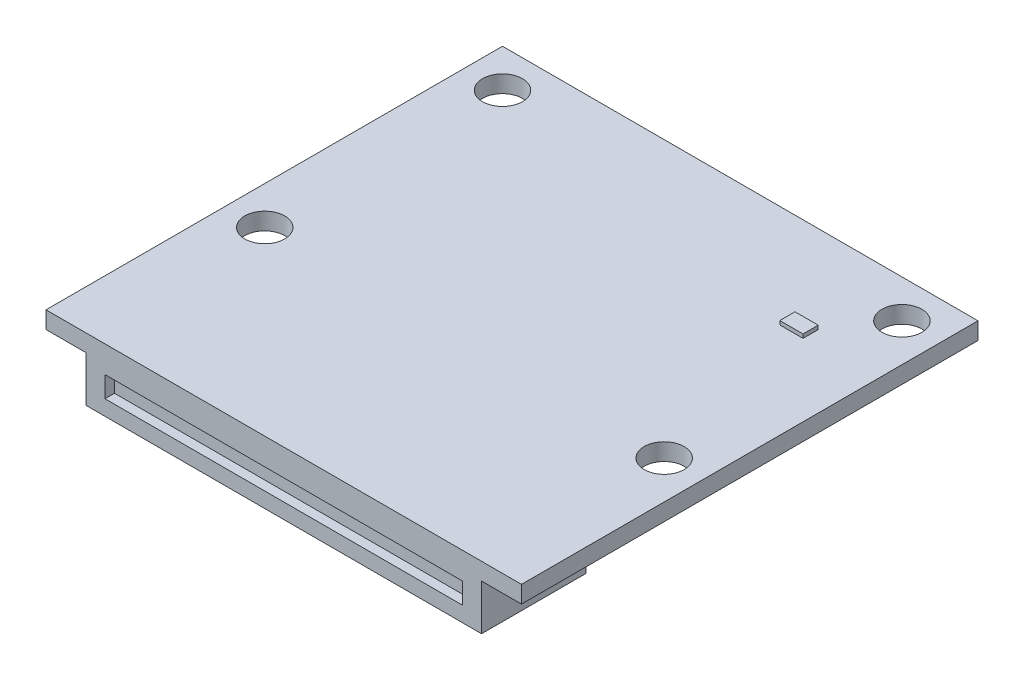
SolidWorks part; units mm, degrees
material "Epoxid, Ungefüllt"
ref_plane "Vorne" through (0, 0, 0) normal (0, 0, 1) x (1, 0, 0)
ref_plane "Oben" through (0, 0, 0) normal (0, 1, 0) x (1, 0, 0)
ref_plane "Rechts" through (0, 0, 0) normal (1, 0, 0) x (0, 0, -1)
sketch "Skizze1" plane through (0, 0, 0) normal (0, 1, 0) x (1, 0, 0)
  line L0 (0, 14.5) -> (0, -9.5) construction
  line L1 (-12.5, 14.5) -> (12.5, 14.5)
  line L2 (-12.5, 14.5) -> (-12.5, -9.5)
  line L3 (-12.5, -9.5) -> (12.5, -9.5)
  line L4 (12.5, 14.5) -> (12.5, -9.5)
extrude "PCB" add sketch "Skizze1" against normal blind 0.9
sketch "Skizze2" plane through (0, 0, 0) normal (0, 1, 0) x (1, 0, 0)
  line L0 (12.5, 14.5) -> (-12.5, 14.5) construction
  line L1 (12.5, -9.5) -> (12.5, 14.5) construction
  line L2 (0, 0) -> (0, 9.3158) construction
  circle A0 centre (10.5, 12.5) radius 1.05
  circle A1 centre (10.5, 0) radius 1.05
  circle A2 centre (-10.5, 0) radius 1.05
  circle A3 centre (-10.5, 12.5) radius 1.05
extrude "Mounting_Holes" cut sketch "Skizze2" against normal through all
sketch "Skizze3" plane through (0, -0.9, 0) normal (0, -1, 0) x (1, 0, 0)
  line L0 (0, 4) -> (0, 0) construction
  line L1 (-10.4, 9.5) -> (10.4, 9.5)
  line L2 (-10.4, 9.5) -> (-10.4, 4)
  line L3 (-10.4, 4) -> (10.4, 4)
  line L4 (10.4, 9.5) -> (10.4, 4)
  line L5 (-12.5, 9.5) -> (12.5, 9.5) construction
extrude "Connector_closed" add sketch "Skizze3" along normal blind 2.4
sketch "Esquisse1" plane through (0, 0, 0) normal (0, 1, 0) x (1, 0, 0)
  line L0 (12.5, 14.5) -> (-12.5, 14.5) construction
  line L1 (8.7, 9.1) -> (7.48, 9.1)
  line L2 (8.7, 9.1) -> (8.7, 9.9)
  line L3 (8.7, 9.9) -> (7.48, 9.9)
  line L4 (7.48, 9.1) -> (7.48, 9.9)
  line L5 (12.5, -9.5) -> (12.5, 14.5) construction
extrude "Status LED" add sketch "Esquisse1" along normal blind 0.2
sketch "Esquisse3" plane through (0, 0, 9.5) normal (0, 0, 1) x (1, 0, 0)
  line L0 (-10.4, -3.3) -> (-10.4, -0.9) construction
  line L1 (-9.4, -1.4) -> (9.4, -1.4)
  line L2 (-9.4, -1.4) -> (-9.4, -2.5)
  line L3 (-9.4, -2.5) -> (9.4, -2.5)
  line L4 (9.4, -1.4) -> (9.4, -2.5)
  line L5 (10.4, -3.3) -> (10.4, -0.9) construction
  line L6 (10.4, -3.3) -> (-10.4, -3.3) construction
  line L7 (-12.5, 0) -> (12.5, 0) construction
extrude "Enlèv. mat.-Extru.1" cut sketch "Esquisse3" against normal blind 0.5
